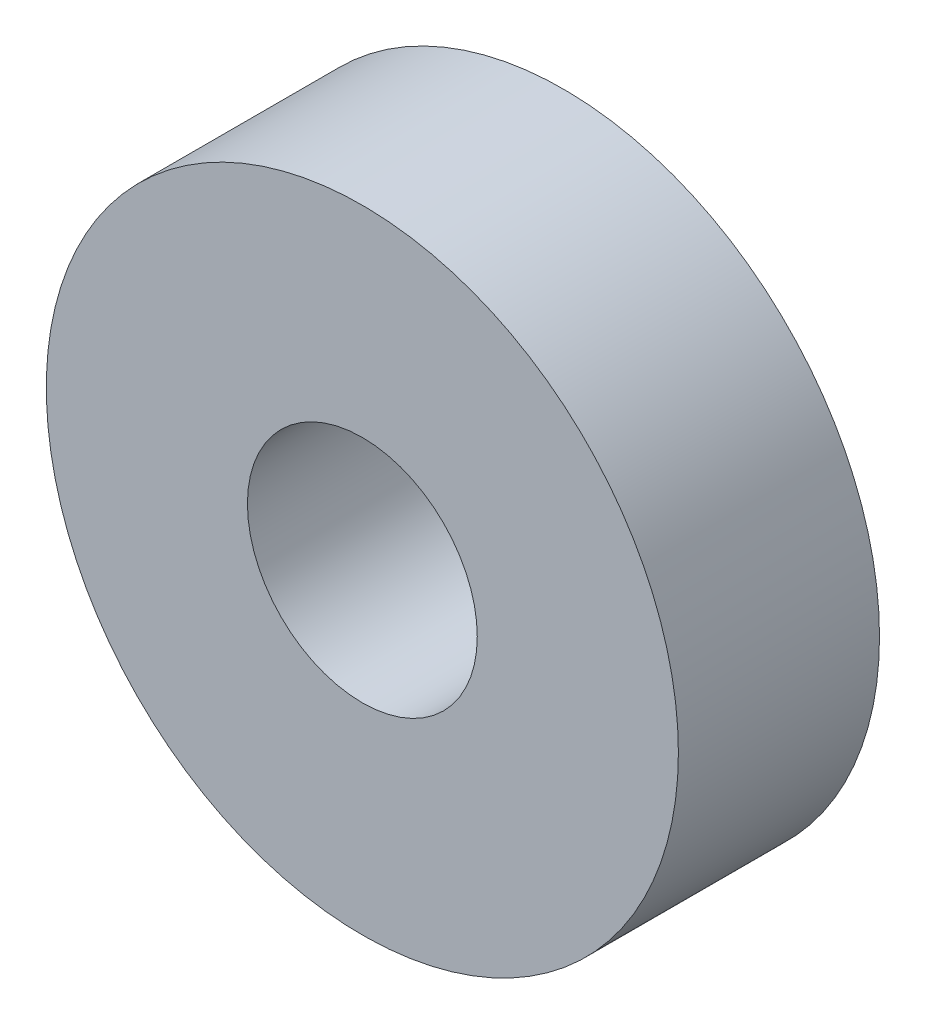
SolidWorks part; units mm, degrees
ref_plane "Plan de face" through (0, 0, 0) normal (0, 0, 1) x (1, 0, 0)
ref_plane "Plan de dessus" through (0, 0, 0) normal (0, 1, 0) x (1, 0, 0)
ref_plane "Plan de droite" through (0, 0, 0) normal (1, 0, 0) x (0, 0, -1)
sketch "Esquisse1" plane through (0, 0, 0) normal (0, 0, 1) x (1, 0, 0)
  circle A0 centre (0, 0) radius 4
  circle A1 centre (0, 0) radius 11
extrude "Extrusion1" add sketch "Esquisse1" along normal blind 7
